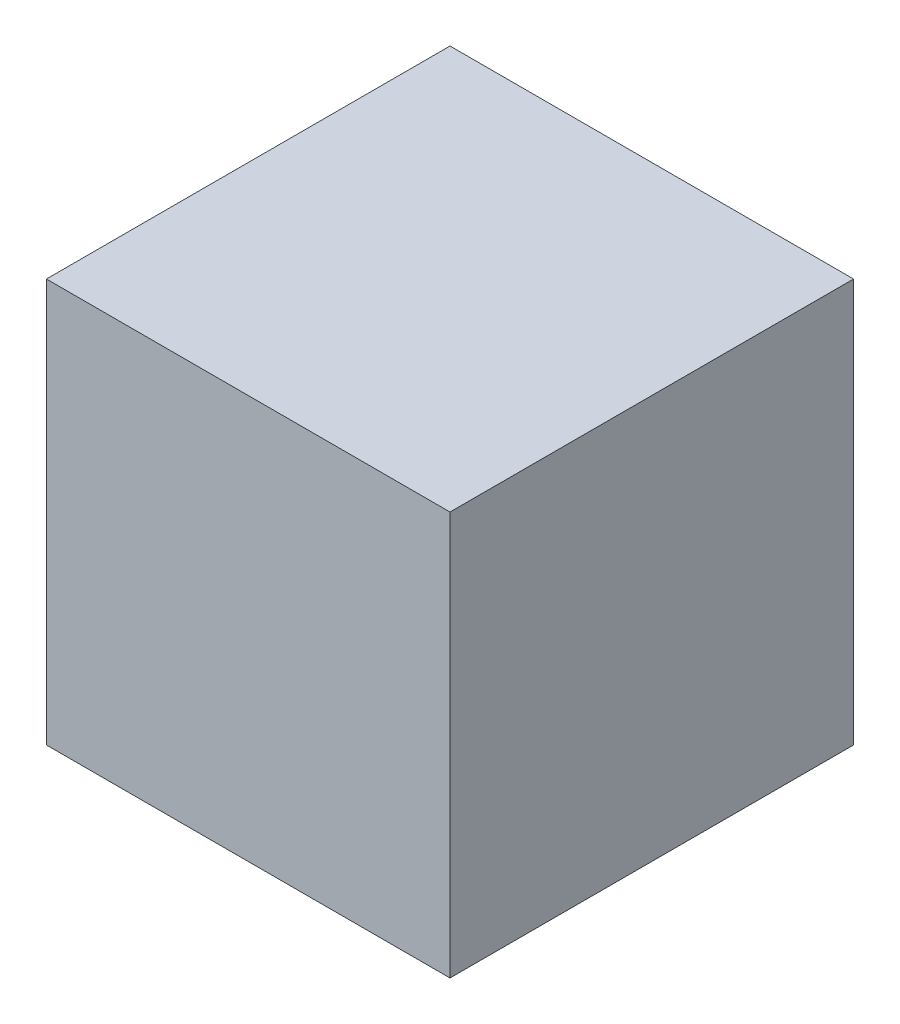
SolidWorks part; units mm, degrees
ref_plane "Plano frontal" through (0, 0, 0) normal (0, 0, 1) x (1, 0, 0)
ref_plane "Plano superior" through (0, 0, 0) normal (0, 1, 0) x (1, 0, 0)
ref_plane "Plano direito" through (0, 0, 0) normal (1, 0, 0) x (0, 0, -1)
sketch "Esboço1" plane through (0, 0, 0) normal (0, 0, 1) x (1, 0, 0)
  line L1 (-5, 5) -> (5, 5)
  line L2 (-5, 5) -> (-5, -5)
  line L3 (-5, -5) -> (5, -5)
  line L4 (5, 5) -> (5, -5)
  line L5 (-5, 5) -> (5, -5) construction
  line L6 (-5, -5) -> (5, 5) construction
  point P0 (0, 0)
  dimension "D1" = 10
  dimension "D2" = 10
extrude "Ressalto-extrusão1" add sketch "Esboço1" along normal blind 10
